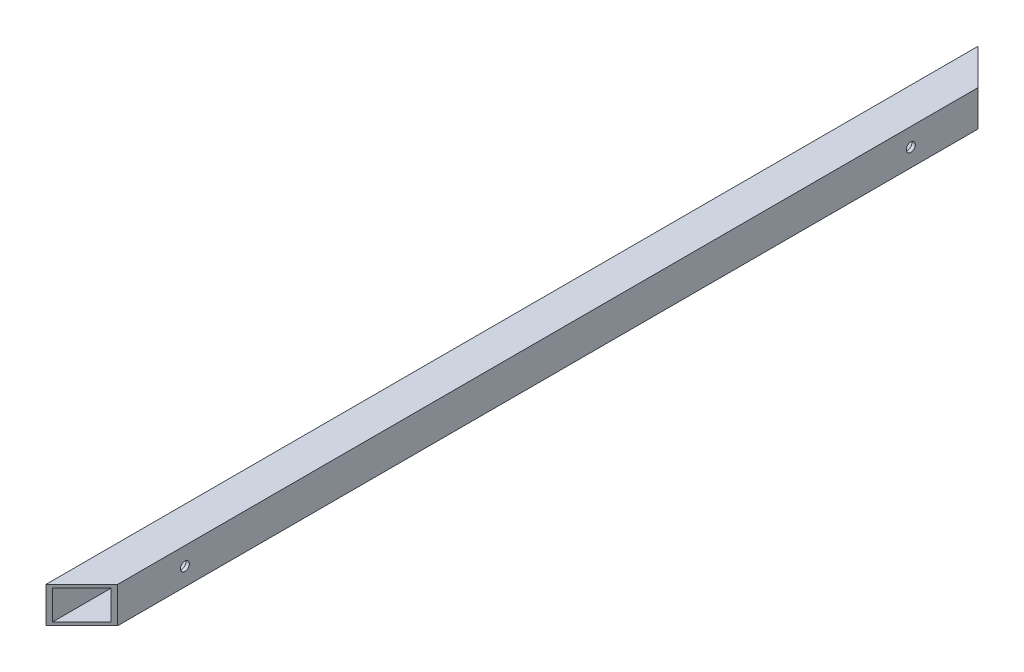
SolidWorks part; units mm, degrees
ref_plane "Front Plane" through (0, 0, 0) normal (0, 0, 1) x (1, 0, 0)
ref_plane "Top Plane" through (0, 0, 0) normal (0, 1, 0) x (1, 0, 0)
ref_plane "Right Plane" through (0, 0, 0) normal (1, 0, 0) x (0, 0, -1)
sketch "Sketch1" plane through (0, 0, 0) normal (0, 0, 1) x (1, 0, 0)
  line L0 (-279.4, 1117.6) -> (-279.4, -50.8) construction
  line L1 (-279.4, 984.25) -> (-228.6, 984.25)
  line L2 (-279.4, 984.25) -> (-279.4, 933.45)
  line L3 (-279.4, 933.45) -> (-228.6, 933.45)
  line L4 (-228.6, 984.25) -> (-228.6, 933.45)
  line L5 (387.6675, 0) -> (-387.6675, 0) construction
  dimension "D1" = 50.8
  dimension "D2" = 984.25
extrude "Extrude-Thin1" add sketch "Sketch1" along normal mid plane 1320.8 thin
sketch "Sketch3" plane through (0, 933.45, 0) normal (0, -1, 0) x (1, 0, 0)
  line L0 (-279.4, 0) -> (133.0059, 0) construction
  line L1 (-279.4, 660.4) -> (-279.4, -660.4) construction
  line L2 (304.8, 0) -> (-122.7933, 0) construction
  line L3 (-279.4, 660.4) -> (-228.6, 609.6)
  line L4 (-228.6, 660.4) -> (-228.6, -660.4) construction
  line L5 (-228.6, 609.6) -> (-228.6, 660.4)
  line L6 (-228.6, 660.4) -> (-279.4, 660.4)
  line L7 (-279.4, -660.4) -> (-228.6, -609.6)
  line L8 (-228.6, -609.6) -> (-228.6, -660.4)
  line L9 (-228.6, -660.4) -> (-279.4, -660.4)
extrude "Cut-Extrude1" cut sketch "Sketch3" against normal through all
sketch "Sketch4" plane through (-279.4, 0, 0) normal (-1, 0, 0) x (0, 0, 1)
  line L0 (0, 0) -> (0, 1517.5653) construction
  line L1 (0, 0) -> (0, 1517.5653) construction
  circle A0 centre (514.35, 958.85) radius 6.35
  circle A1 centre (-514.35, 958.85) radius 6.35
  dimension "D1" = 12.7
extrude "Cut-Extrude2" cut sketch "Sketch4" against normal through all
